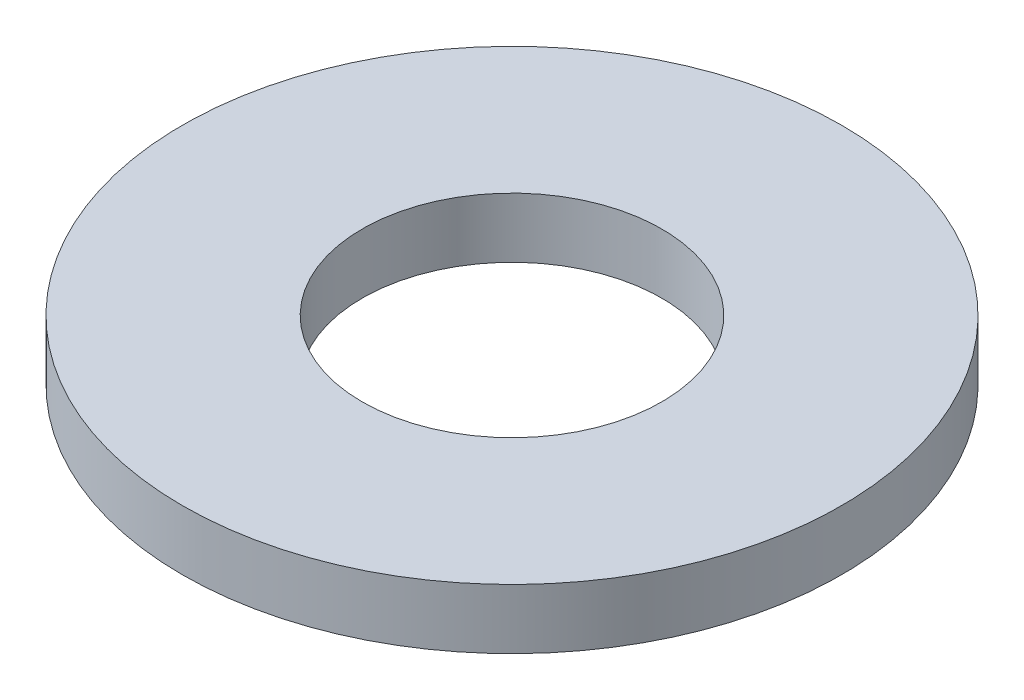
SolidWorks part; units mm, degrees
ref_plane "Plan de face" through (0, 0, 0) normal (0, 0, 1) x (1, 0, 0)
ref_plane "Plan de dessus" through (0, 0, 0) normal (0, 1, 0) x (1, 0, 0)
ref_plane "Plan de droite" through (0, 0, 0) normal (1, 0, 0) x (0, 0, -1)
sketch "Esquisse1" plane through (0, 0, 0) normal (0, 1, 0) x (1, 0, 0)
  circle A0 centre (0, 0) radius 5.5
  circle A1 centre (0, 0) radius 2.5
  dimension "D1" = 5
  dimension "D2" = 11
extrude "Boss.-Extru.1" add sketch "Esquisse1" along normal blind 1
